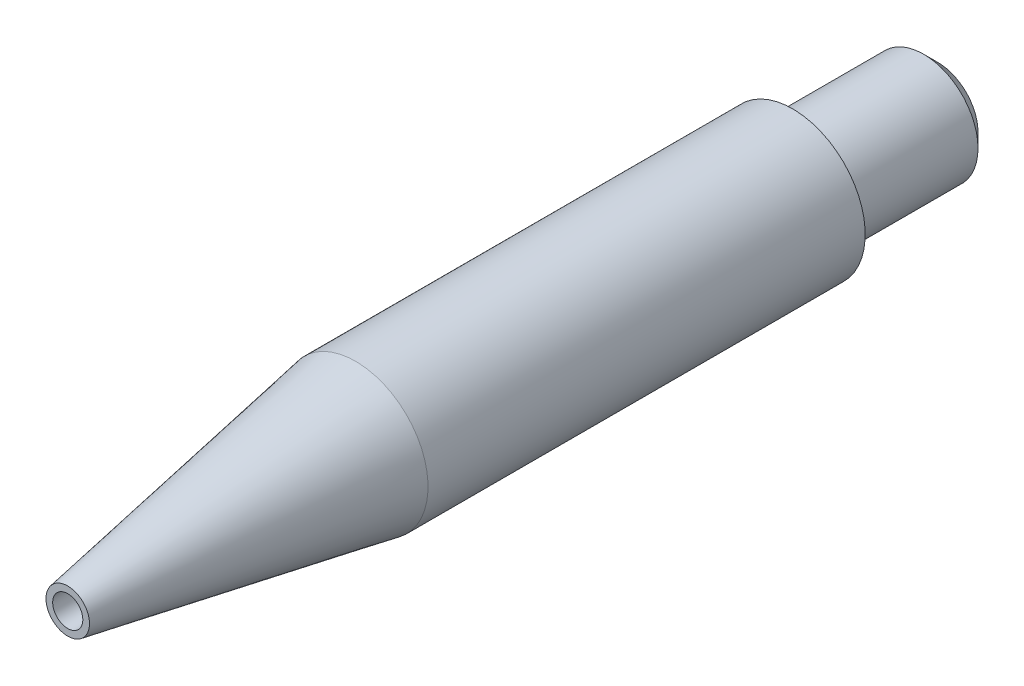
SolidWorks part; units mm, degrees
material "6061 Alloy"
ref_plane "Front Plane" through (0, 0, 0) normal (0, 0, 1) x (1, 0, 0)
ref_plane "Top Plane" through (0, 0, 0) normal (0, 1, 0) x (1, 0, 0)
ref_plane "Right Plane" through (0, 0, 0) normal (1, 0, 0) x (0, 0, -1)
sketch "Sketch19" plane through (0, 0, 0) normal (0, 1, 0) x (1, 0, 0)
  line L0 (0, -0.4662) -> (0, 20.0331) construction
sketch "Sketch1" plane through (0, 0, 0) normal (0, 0, 1) x (1, 0, 0)
  circle A0 centre (0, 0) radius 6.35
  dimension "D1" = 12.7
extrude "Boss-Extrude1" add sketch "Sketch1" along normal blind 76.2
sketch "Sketch7" plane through (0, 0, 0) normal (0, 1, 0) x (1, 0, 0)
  line L0 (6.35, -76.2) -> (6.35, -50.9912)
  line L1 (6.35, -76.2) -> (1.905, -76.2)
  line L2 (-6.35, -76.2) -> (6.35, -76.2) construction
  line L8 (6.35, -76.2) -> (6.35, 0) construction
  line L9 (1.905, -76.2) -> (6.35, -50.9912)
  line L10 (0, 47.574) -> (0, -47.574) construction
  dimension "D1" = 10
  dimension "D2" = 4.445
revolve "Cut-Revolve1" cut sketch "Sketch7" angle 360 about L10
sketch "Sketch8" plane through (0, 0, 76.2) normal (0, 0, 1) x (1, 0, 0)
  circle A0 centre (0, 0) radius 1.3208
  dimension "D1" = 2.6416
extrude "Cut-Extrude1" cut sketch "Sketch8" against normal through all
sketch "Sketch10" plane through (0, 0, 0) normal (0, 0, -1) x (-1, 0, 0)
  circle A0 centre (0, 0) radius 4.7625
  circle A1 centre (0, 0) radius 6.35 construction
  circle A2 centre (0, 0) radius 6.35
  dimension "D1" = 9.525
extrude "Cut-Extrude2" cut sketch "Sketch10" against normal blind 12.7
hole_wizard "1/4 (0.25) Diameter Hole1" positions "3DSketch2" profile "Sketch17" hole size "1/4" standard "ANSI Inch"
sketch3d "3DSketch2"
  point P0 (0, 0, 0)
sketch "Sketch17" plane through (0, 0, 0) normal (1, 0, 0) x (0, 1, 0)
  line L0 (0, 0) -> (0, 65.4077)
  line L1 (0, 65.4077) -> (3.175, 63.5)
  line L2 (3.175, 63.5) -> (3.175, 0)
  line L5 (3.175, 0) -> (0, 0)
  line L10 (0, 65.4077) -> (-3.175, 63.5) construction
  line L11 (0, -6.35) -> (0, 107.95) construction
  dimension "Hole Dia." = 6.35
  dimension "Hole Depth" = 63.5
  dimension "Drill Angle" = 118
sketch "Sketch18" plane through (0, 0, 0) normal (0, 1, 0) x (1, 0, 0)
  line L0 (4.7625, -12.7) -> (4.7625, 0) construction
  line L1 (6.35, -12.7) -> (-6.35, -12.7) construction
  line L2 (4.7625, -12.7) -> (4.7625, 0) construction
  line L3 (6.35, -12.7) -> (-6.35, -12.7) construction
  line L4 (4.7625, -12.7) -> (4.1656, -12.7)
  line L5 (4.7625, -11.684) -> (4.1656, -11.684)
  line L6 (4.7625, -12.7) -> (4.7625, -11.684)
  arc A0 (4.1656, -12.7) -> (4.1656, -11.684) centre (4.1656, -12.192) cw
  point P9 (3.6576, -12.192)
  dimension "D2" = 1.1049
  dimension "D3" = 1.016
revolve "Cut-Revolve2" cut sketch "Sketch18" angle 360 about L0
sketch "Sketch20" plane through (0, 0, 0) normal (0, 1, 0) x (1, 0, 0)
  line L0 (4.7625, -11.684) -> (4.7625, 0) construction
  line L1 (4.7625, 0) -> (-4.7625, 0) construction
  line L2 (4.7625, -11.684) -> (4.7625, 0) construction
  line L3 (4.7625, 0) -> (-4.7625, 0) construction
  line L4 (4.7625, 0) -> (4.7625, -1.2319)
  line L5 (4.7625, -1.2319) -> (3.5306, 0)
  line L6 (3.5306, 0) -> (4.7625, 0)
  dimension "D1" = 1.2319
revolve "Cut-Revolve3" cut sketch "Sketch20" angle 360 about L0
